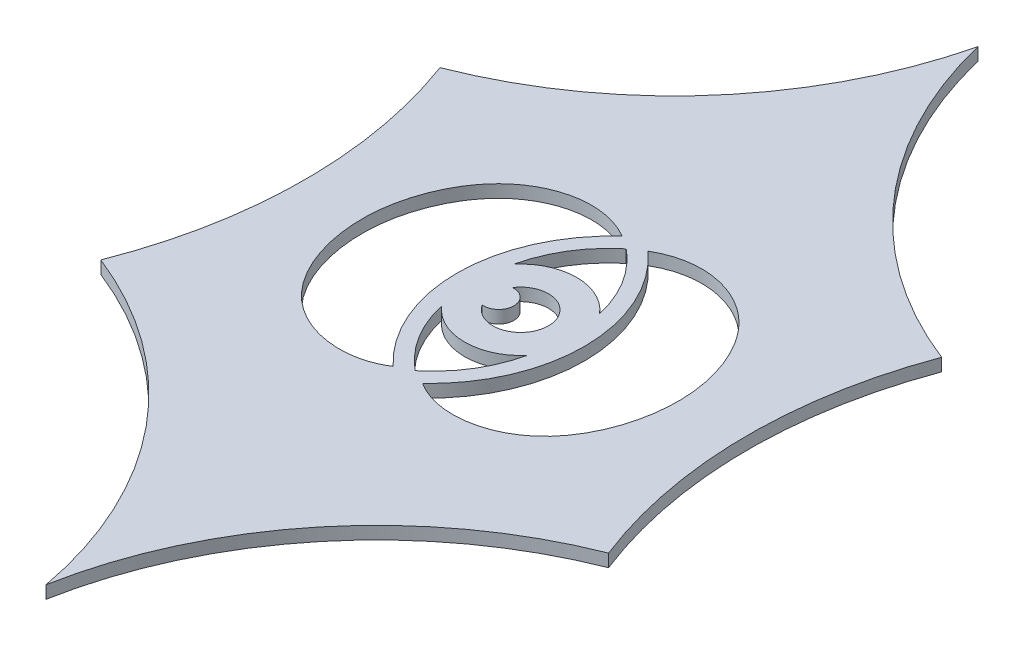
SolidWorks part; units mm, degrees
ref_plane "Front" through (0, 0, 0) normal (0, 0, 1) x (1, 0, 0)
ref_plane "Top" through (0, 0, 0) normal (0, 1, 0) x (1, 0, 0)
ref_plane "Right" through (0, 0, 0) normal (1, 0, 0) x (0, 0, -1)
sketch "Эскиз2" plane through (0, 0, 0) normal (0, 1, 0) x (1, 0, 0)
  line L0 (27, -175) -> (-17, -175) construction
  line L1 (27, -28) -> (-17, -28) construction
  line L2 (-35.603, -115.1472) -> (-29.2391, -121.5111) construction
  line L3 (5, -175) -> (5, -28) construction
  arc A0 (-34.5608, -73.2947) -> (-35.0422, -126.311) centre (-104.2196, -99.1725) cw
  arc A1 (-95, -95) -> (0, 0) centre (-95, 0) ccw construction
  arc A2 (0, -200) -> (-95, -105) centre (-95, -200) ccw construction
  arc A3 (-35.0422, -126.311) -> (5, -175) centre (-58.9266, -186.7638) cw
  arc A4 (5, -28) -> (-34.5608, -73.2947) centre (-58.1831, -12.739) cw
  arc A6 (45.0422, -126.311) -> (5, -175) centre (68.9266, -186.7638) ccw
  arc A7 (44.5608, -73.2947) -> (45.0422, -126.311) centre (114.2196, -99.1725) ccw
  arc A8 (5, -28) -> (44.5608, -73.2947) centre (68.1831, -12.739) ccw
  point P16 (-32.421, -118.3292)
  dimension "D1" = 65
extrude "Бобышка-Вытянуть1" add sketch "Эскиз2" along normal blind 2
sketch "Эскиз5" plane through (0, 2, 0) normal (0, 1, 0) x (1, 0, 0)
  line L0 (4.8758, -100.0074) -> (4.8758, -83.3685) construction
  line L1 (4.8758, -100.0074) -> (13.7132, -100.0074) construction
  circle A0 centre (4.8758, -100.0074) radius 4.388
  circle A1 centre (1.4085, -100.0074) radius 2.3943
  circle A2 centre (4.8758, -100.0074) radius 8.8374
  circle A3 centre (-9.4713, -100.0074) radius 24.3844
  circle A4 centre (19.2229, -100.0074) radius 24.3844
  spline S0 degree 2 poles (11.6463, -94.3276) (10.1133, -87.7186) (4.8758, -83.3685) knots 0 0 0 1 1 1
  spline S1 degree 2 poles (-1.8948, -94.3276) (-0.3617, -87.7186) (4.8758, -83.3685) knots 0 0 0 1 1 1
  spline S2 degree 2 poles (-1.8948, -105.6871) (-0.3617, -112.2961) (4.8758, -116.6462) knots 0 0 0 1 1 1
  spline S3 degree 2 poles (11.6463, -105.6871) (10.1133, -112.2961) (4.8758, -116.6462) knots 0 0 0 1 1 1
  spline S4 degree 3 poles (6.9168, -81.951) (12.3076, -78.7875) (22.3893, -80.7933) (29.7314, -92.8111) (30.4347, -105.1167) (25.6438, -115.0017) (17.0915, -120.2272) (10.6462, -120.0562) (7.2068, -117.7961) knots 0 0 0 0 0.238043 0.386081 0.575652 0.751375 0.825495 1 1 1 1
  spline S5 degree 3 poles (2.8348, -81.951) (-2.5561, -78.7875) (-12.6378, -80.7933) (-19.9798, -92.8111) (-20.6831, -105.1167) (-15.8923, -115.0017) (-7.3399, -120.2272) (-0.8946, -120.0562) (2.5448, -117.7961) knots 0 0 0 0 0.238043 0.386081 0.575652 0.751375 0.825495 1 1 1 1
extrude "Вырез-Вытянуть2" cut sketch "Эскиз5" against normal through all contours A4 S5 | S1 A2 S0 | S3 A2 S2 | A1 A0 | S4 A3
